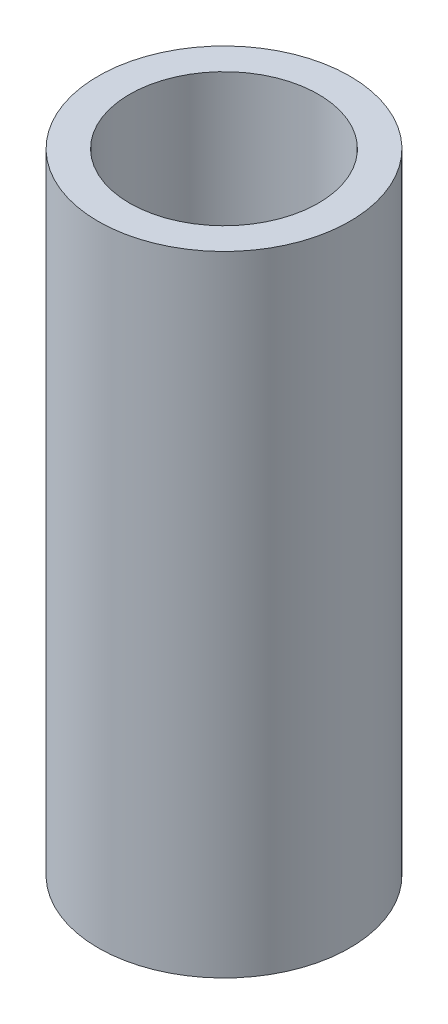
SolidWorks part; units mm, degrees
material "PVC 0.007 Plasticized"
ref_plane "Front Plane" through (0, 0, 0) normal (0, 0, 1) x (1, 0, 0)
ref_plane "Top Plane" through (0, 0, 0) normal (0, 1, 0) x (1, 0, 0)
ref_plane "Right Plane" through (0, 0, 0) normal (1, 0, 0) x (0, 0, -1)
sketch "Sketch1" plane through (0, 0, 0) normal (0, 1, 0) x (1, 0, 0)
  circle A0 centre (0, 0) radius 9.525
  circle A1 centre (0, 0) radius 12.7
  dimension "D1" = 19.05
  dimension "D2" = 25.4
extrude "Boss-Extrude1" add sketch "Sketch1" along normal blind 63.5 contours A1 A0
